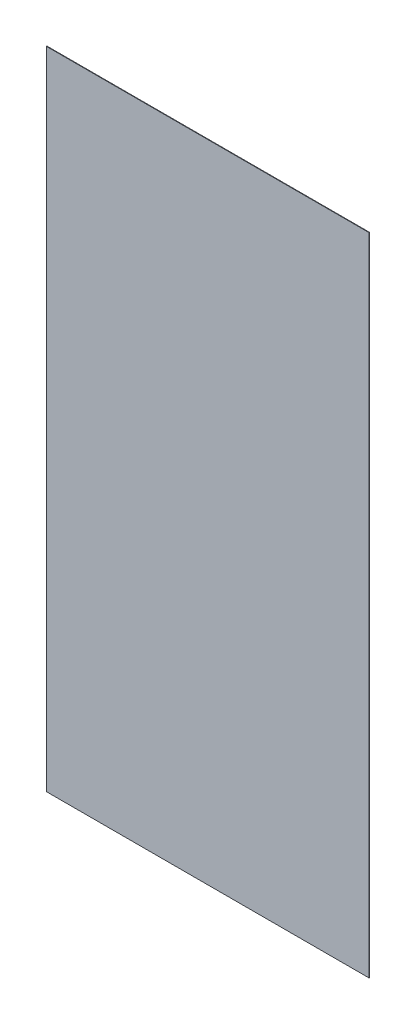
SolidWorks part; units mm, degrees
ref_plane "Plan de face" through (0, 0, 0) normal (0, 0, 1) x (1, 0, 0)
ref_plane "Plan de dessus" through (0, 0, 0) normal (0, 1, 0) x (1, 0, 0)
ref_plane "Plan de droite" through (0, 0, 0) normal (1, 0, 0) x (0, 0, -1)
sketch "Esquisse1" plane through (0, 0, 0) normal (0, 0, 1) x (1, 0, 0)
  line L1 (-625, 1250) -> (625, 1250)
  line L2 (-625, 1250) -> (-625, -1250)
  line L3 (-625, -1250) -> (625, -1250)
  line L4 (625, 1250) -> (625, -1250)
  line L5 (-625, 1250) -> (625, -1250) construction
  line L6 (-625, -1250) -> (625, 1250) construction
  point P0 (0, 0)
  dimension "D1" = 1250
  dimension "D2" = 2500
extrude "Boss.-Extru.1" add sketch "Esquisse1" along normal blind 2
